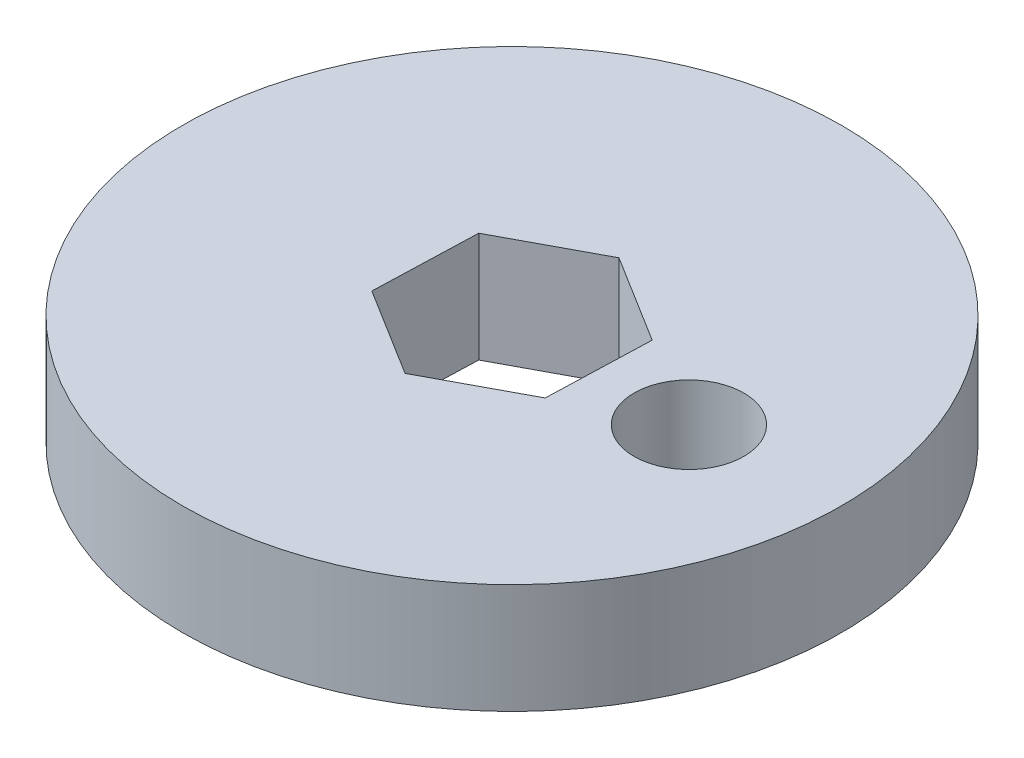
SolidWorks part; units mm, degrees
ref_plane "Front Plane" through (0, 0, 0) normal (0, 0, 1) x (1, 0, 0)
ref_plane "Top Plane" through (0, 0, 0) normal (0, 1, 0) x (1, 0, 0)
ref_plane "Right Plane" through (0, 0, 0) normal (1, 0, 0) x (0, 0, -1)
sketch "Sketch1" plane through (0, 0, 0) normal (0, 1, 0) x (1, 0, 0)
  line L0 (2.4953, 1.333) -> (2.402, -1.4945)
  line L1 (2.402, -1.4945) -> (-0.0933, -2.8275)
  line L2 (-0.0933, -2.8275) -> (-2.4953, -1.333)
  line L3 (-2.4953, -1.333) -> (-2.402, 1.4945)
  line L4 (-2.402, 1.4945) -> (0.0933, 2.8275)
  line L5 (0.0933, 2.8275) -> (2.4953, 1.333)
  circle A0 centre (0, 0) radius 9
  circle A1 centre (4.9973, -0.1648) radius 1.5
  dimension "D1" = 18
  dimension "D3" = 3
  dimension "D2" = 4.9973
extrude "Boss-Extrude1" add sketch "Sketch1" along normal blind 3
